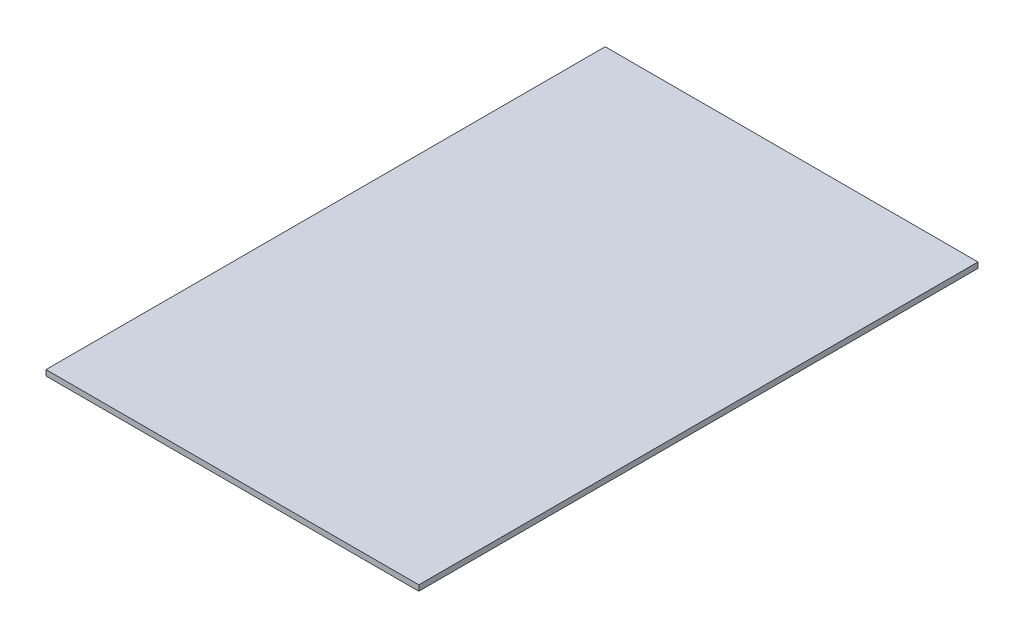
SolidWorks part; units mm, degrees
ref_plane "Front Plane" through (0, 0, 0) normal (0, 0, 1) x (1, 0, 0)
ref_plane "Top Plane" through (0, 0, 0) normal (0, 1, 0) x (1, 0, 0)
ref_plane "Right Plane" through (0, 0, 0) normal (1, 0, 0) x (0, 0, -1)
sketch "Sketch1" plane through (0, 0, 0) normal (0, 1, 0) x (1, 0, 0)
  line L1 (100, 150) -> (-100, 150)
  line L2 (100, 150) -> (100, -150)
  line L3 (100, -150) -> (-100, -150)
  line L4 (-100, 150) -> (-100, -150)
  line L5 (100, 150) -> (-100, -150) construction
  line L6 (100, -150) -> (-100, 150) construction
  point P0 (0, 0)
  dimension "D1" = 200
  dimension "D2" = 300
extrude "Boss-Extrude1" add sketch "Sketch1" along normal blind 3
